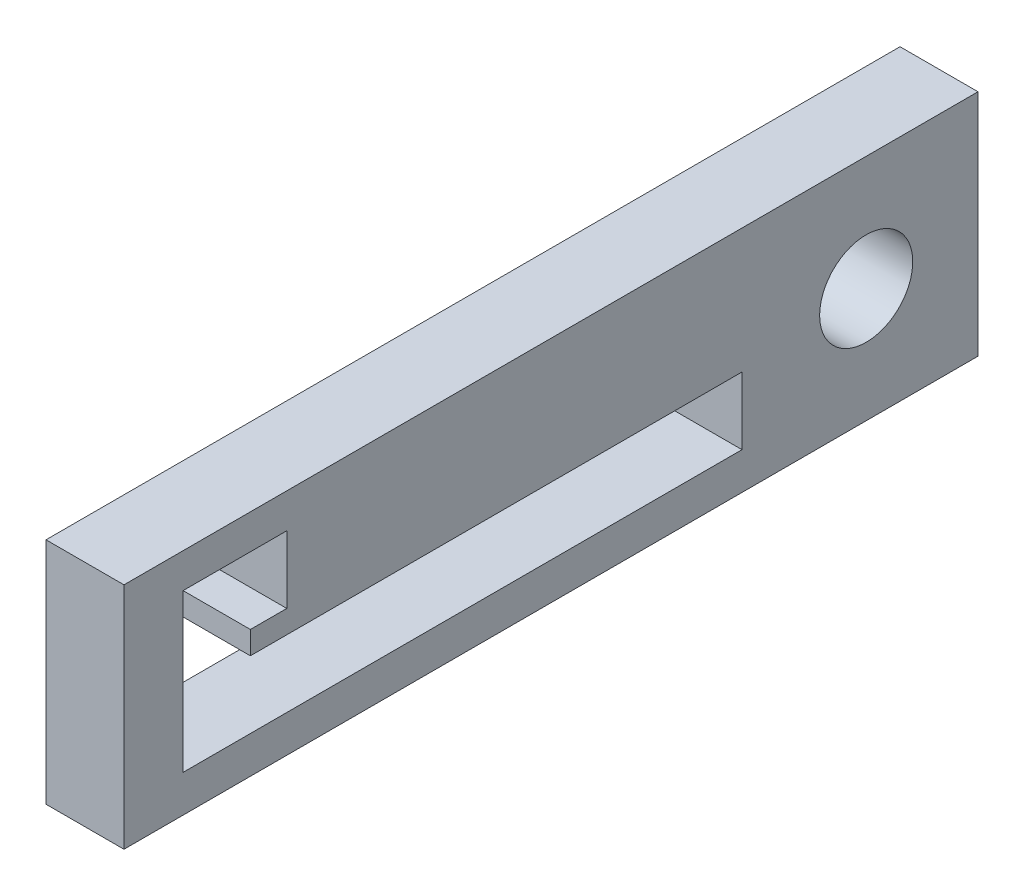
SolidWorks part; units mm, degrees
ref_plane "Front Plane" through (0, 0, 0) normal (0, 0, 1) x (1, 0, 0)
ref_plane "Top Plane" through (0, 0, 0) normal (0, 1, 0) x (1, 0, 0)
ref_plane "Right Plane" through (0, 0, 0) normal (1, 0, 0) x (0, 0, -1)
sketch "Sketch2" plane through (0, 0, 0) normal (-1, 0, 0) x (0, 0, 1)
  line L1 (-21.3901, 26.9999) -> (48.159, 26.9999)
  line L2 (-21.3901, 26.9999) -> (-21.3901, 45.6523)
  line L3 (-21.3901, 45.6523) -> (48.159, 45.6523)
  line L4 (48.159, 26.9999) -> (48.159, 45.6523)
  line L5 (-2.1698, 35.497) -> (37.865, 35.497)
  line L6 (-2.1698, 35.497) -> (-2.1698, 30.0185)
  line L9 (37.865, 37.3559) -> (34.9002, 37.3559)
  line L10 (34.9002, 37.3559) -> (34.9002, 42.8344)
  line L11 (34.9002, 42.8344) -> (43.3435, 42.8344)
  line L12 (43.3435, 42.8344) -> (43.3435, 30.0185)
  line L15 (37.865, 30.0185) -> (43.3435, 30.0185)
  line L16 (37.865, 30.0185) -> (-2.1698, 30.0185)
  line L18 (37.865, 37.3559) -> (37.865, 35.497)
  line L26 (56.118, 37.2895) -> (57.8241, 32.0834) construction
  circle A0 centre (-12.285, 36.3261) radius 3.7923
  point P37 (-21.3901, 36.3261)
extrude "Boss-Extrude1" add sketch "Sketch2" along normal blind 6.35 contours L16 L6 L5 L9 L10 L11 L12 L15
sketch "Sketch5" plane through (-6.35, 0, 0) normal (-1, 0, 0) x (0, 0, 1)
  line L10 (40.405, 39.8959) -> (34.9002, 39.8959)
  line L11 (40.405, 32.957) -> (40.405, 39.8959)
  line L12 (-2.1698, 32.957) -> (40.405, 32.957)
  line L13 (37.865, 39.8959) -> (34.9002, 39.8959)
  line L14 (40.405, 35.497) -> (40.405, 37.3559)
  line L15 (-2.1698, 32.957) -> (37.865, 32.957)
  arc A0 (40.405, 35.497) -> (37.865, 32.957) centre (37.865, 35.497) cw
  arc A1 (40.405, 37.3559) -> (37.865, 39.8959) centre (37.865, 37.3559) ccw
  dimension "D2" = 2.54
  dimension "D3" = 2.54
  dimension "D1" = 2.54
sketch "Sketch3" plane through (0, 0, 0) normal (1, 0, 0) x (0, 0, -1)
  line L6 (2.1698, 32.957) -> (-40.405, 32.957)
  line L7 (-40.405, 32.957) -> (-40.405, 39.8959)
  line L8 (-40.405, 39.8959) -> (-34.9002, 39.8959)
  line L9 (2.1698, 32.957) -> (-37.865, 32.957)
  line L10 (-40.405, 35.497) -> (-40.405, 37.3559)
  line L11 (-37.865, 39.8959) -> (-34.9002, 39.8959)
  arc A0 (-40.405, 37.3559) -> (-37.865, 39.8959) centre (-37.865, 37.3559) cw
  arc A1 (-40.405, 35.497) -> (-37.865, 32.957) centre (-37.865, 35.497) ccw
  dimension "D2" = 2.54
  dimension "D3" = 2.54
  dimension "D1" = 2.54
